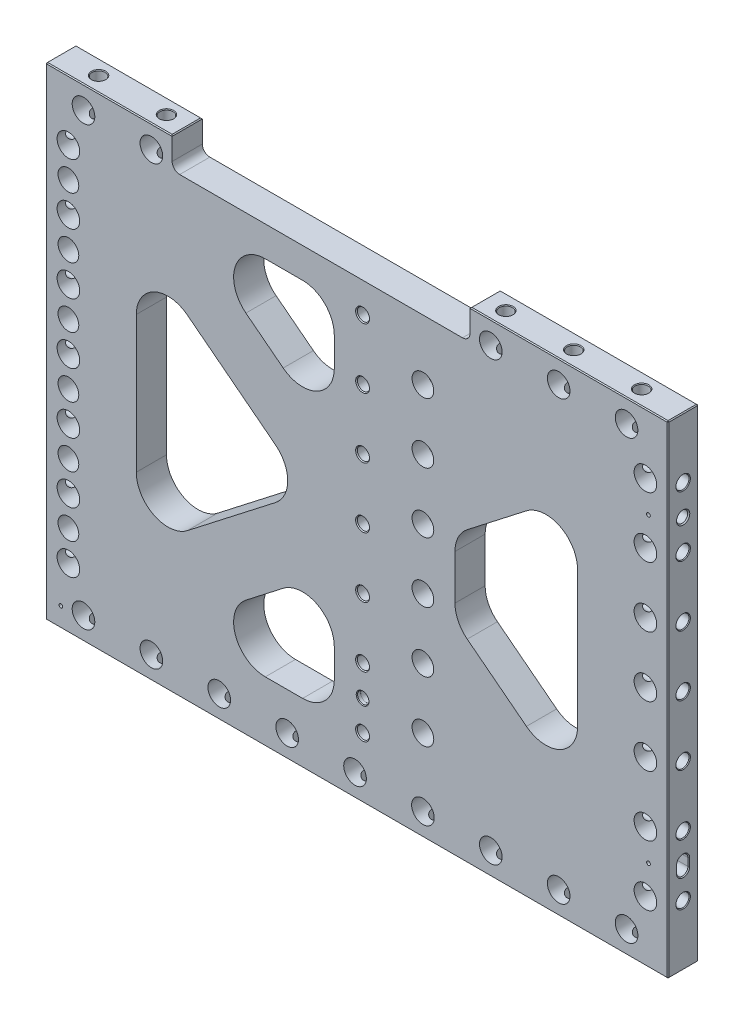
SolidWorks part; units mm, degrees
material "6061-T6 Al"
ref_plane "Front Plane" through (0, 0, 0) normal (0, 0, 1) x (1, 0, 0)
ref_plane "Top Plane" through (0, 0, 0) normal (0, 1, 0) x (1, 0, 0)
ref_plane "Right Plane" through (0, 0, 0) normal (1, 0, 0) x (0, 0, -1)
sketch "Sketch2" plane through (0, 0, 0) normal (0, 0, 1) x (1, 0, 0)
  line L0 (-261.9375, -203.2) -> (261.9375, 203.2) construction
  line L1 (-261.9375, 203.2) -> (261.9375, 203.2)
  line L2 (-261.9375, 203.2) -> (-261.9375, -203.2)
  line L3 (-261.9375, -203.2) -> (261.9375, -203.2)
  line L4 (261.9375, 203.2) -> (261.9375, -203.2)
  point P4 (0, 0)
  dimension "D1" = 523.875
  dimension "D2" = 406.4
extrude "Extrude1" add sketch "Sketch2" along normal mid plane 25.4
sketch "Sketch8" plane through (0, 0, 12.7) normal (0, 0, 1) x (1, 0, 0)
  line L0 (-261.9375, 203.2) -> (261.9375, -203.2) construction
  line L1 (261.9375, 203.2) -> (-261.9375, -203.2) construction
  line L2 (-185.7375, 111.9405) -> (-41.4392, 0)
  line L3 (-41.4392, 0) -> (-185.7375, -111.9405)
  line L4 (-185.7375, -111.9405) -> (-185.7375, 111.9405)
  line L5 (-155.0139, 152.4) -> (0, 32.1468)
  line L6 (0, 32.1468) -> (155.0139, 152.4)
  line L7 (155.0139, 152.4) -> (-155.0139, 152.4)
  line L8 (185.7375, 111.9405) -> (185.7375, -111.9405)
  line L9 (185.7375, -111.9405) -> (41.4392, 0)
  line L10 (41.4392, 0) -> (185.7375, 111.9405)
  line L11 (0, -32.1468) -> (-155.0139, -152.4)
  line L12 (-155.0139, -152.4) -> (155.0139, -152.4)
  line L13 (155.0139, -152.4) -> (0, -32.1468)
  line L14 (0, -32.1468) -> (-41.4392, 0) construction
  line L15 (-41.4392, 0) -> (0, 32.1468) construction
  line L20 (-261.9375, 203.2) -> (-261.9375, -203.2) construction
  line L21 (261.9375, 203.2) -> (-261.9375, 203.2) construction
  point P19 (-20.7196, 16.0734)
  point P23 (-20.7196, -16.0734)
  point P24 (-261.9375, 0)
  dimension "D1" = 50.8
  dimension "D2" = 76.2
  dimension "D3" = 50.8
extrude "Triangles -- Cut-Extrude2" cut sketch "Sketch8" against normal through all
fillet "Triangles -- Fillet1" radius 26.67 12 edges at (-185.7375, -111.9405, 0) (-41.4392, 0, 0) (-155.0139, -152.4, 0) (155.0139, -152.4, 0) (0, -32.1468, 0) (41.4392, 0, 0) (185.7375, -111.9405, 0) (185.7375, 111.9405, 0) (155.0139, 152.4, 0) (-155.0139, 152.4, 0) (0, 32.1468, 0) (-185.7375, 111.9405, 0)
sketch "Sketch14" plane through (0, 0, 12.7) normal (0, 0, 1) x (1, 0, 0)
  line L0 (261.9375, 203.2) -> (-261.9375, 203.2) construction
  line L1 (-19.05, 203.2) -> (19.05, 203.2)
  line L2 (-19.05, 203.2) -> (-19.05, -203.2)
  line L3 (-19.05, -203.2) -> (19.05, -203.2)
  line L4 (19.05, 203.2) -> (19.05, -203.2)
  line L5 (-261.9375, -203.2) -> (261.9375, -203.2) construction
  line L6 (19.05, 0) -> (-19.05, 0) construction
  point P10 (0, 0)
  dimension "D1" = 38.1
extrude "Extrude3" add sketch "Sketch14" against normal through all
fillet "Fillet1" radius 26.67 8 edges at (19.05, -152.4, 0) (-19.05, -152.4, 0) (-19.05, -46.925, 0) (19.05, -46.925, 0) (19.05, 46.925, 0) (19.05, 152.4, 0) (-19.05, 152.4, 0) (-19.05, 46.925, 0)
hole_wizard "3/4 (0.75) Diameter Hole1" positions "Sketch4" profile "Sketch3" hole size "3/4" standard "Ansi Inch" end condition through all
sketch "Sketch4" plane through (0, 0, 12.7) normal (0, 0, 1) x (1, 0, 0)
  line L3 (0, 0) -> (-242.8875, 0) construction
  line L6 (-261.9375, 203.2) -> (-261.9375, -203.2) construction
  point P0 (-242.8875, 0)
  dimension "D1" = 19.05
sketch "Sketch3" plane through (-242.8875, 0, 12.7) normal (1, 0, 0) x (0, -1, 0)
  line L0 (0, 0) -> (0, 25.4)
  line L1 (0, 25.4) -> (9.525, 25.4)
  line L2 (9.525, 25.4) -> (9.525, 0)
  line L5 (9.525, 0) -> (0, 0)
  line L11 (0, -6.35) -> (0, 107.95) construction
  dimension "Thru Hole Dia." = 19.05
  dimension "Thru Hole Depth" = 25.4
hole_wizard "7/16 (0.4375) Diameter Hole1" positions "Sketch6" profile "Sketch5" hole size "7/16" standard "Ansi Inch"
sketch "Sketch6" plane through (-261.9375, 0, 0) normal (-1, 0, 0) x (0, 0, 1)
  point P0 (0, 0)
sketch "Sketch5" plane through (-261.9375, 0, 0) normal (0, 1, 0) x (0, 0, 1)
  line L0 (0, 0) -> (0, 38.2635)
  line L1 (0, 38.2635) -> (5.5562, 34.925)
  line L2 (5.5562, 34.925) -> (5.5562, 0.6209)
  line L3 (5.5562, 0.6209) -> (6.096, 0)
  line L5 (6.096, 0) -> (0, 0)
  line L6 (-5.5562, 0.6209) -> (-6.096, 0) construction
  line L10 (0, 38.2635) -> (-5.5563, 34.925) construction
  line L11 (0, -6.35) -> (0, 107.95) construction
  dimension "Hole Dia." = 11.1125
  dimension "Hole Depth" = 34.925
  dimension "Near C'Sink Dia." = 12.192
  dimension "Near C'Sink Angle" = 82
  dimension "Drill Angle" = 118
pattern_linear "LPattern3" count 4 spacing 50.8 along (0, 1, 0) count 4 spacing 50.8 along (0, -1, 0) of "7/16 (0.4375) Diameter Hole1", "3/4 (0.75) Diameter Hole1"
mirror "Mirror1" about plane through (0, 0, 0) normal (1, 0, 0) of "LPattern3", "3/4 (0.75) Diameter Hole1", "7/16 (0.4375) Diameter Hole1"
hole_wizard "3/4 (0.75) Diameter Hole2" positions "Sketch11" profile "Sketch10" hole size "3/4" standard "Ansi Inch" end condition through all
sketch "Sketch11" plane through (0, 0, 12.7) normal (0, 0, 1) x (1, 0, 0)
  line L3 (-1.5875, -184.15) -> (-230.1875, -184.15) construction
  line L6 (-261.9375, -203.2) -> (261.9375, -203.2) construction
  point P25 (-230.1875, -184.15)
  dimension "D1" = 19.05
  dimension "D2" = 1.5875
  dimension "D3" = 228.6
sketch "Sketch10" plane through (-230.1875, -184.15, 12.7) normal (1, 0, 0) x (0, -1, 0)
  line L0 (0, 0) -> (0, 25.4)
  line L1 (0, 25.4) -> (9.525, 25.4)
  line L2 (9.525, 25.4) -> (9.525, 0)
  line L5 (9.525, 0) -> (0, 0)
  line L11 (0, -6.35) -> (0, 107.95) construction
  dimension "Thru Hole Dia." = 19.05
  dimension "Thru Hole Depth" = 25.4
hole_wizard "7/16 (0.4375) Diameter Hole2" positions "Sketch13" profile "Sketch12" hole size "7/16" standard "Ansi Inch"
sketch "Sketch13" plane through (0, -203.2, 0) normal (0, -1, 0) x (1, 0, 0)
  point P0 (-230.1875, 0)
sketch "Sketch12" plane through (-230.1875, -203.2, 0) normal (1, 0, 0) x (0, 0, -1)
  line L0 (0, 0) -> (0, 38.2635)
  line L1 (0, 38.2635) -> (5.5562, 34.925)
  line L2 (5.5562, 34.925) -> (5.5562, 0.6209)
  line L3 (5.5562, 0.6209) -> (6.096, 0)
  line L5 (6.096, 0) -> (0, 0)
  line L6 (-5.5562, 0.6209) -> (-6.096, 0) construction
  line L10 (0, 38.2635) -> (-5.5563, 34.925) construction
  line L11 (0, -6.35) -> (0, 107.95) construction
  dimension "Hole Dia." = 11.1125
  dimension "Hole Depth" = 34.925
  dimension "Near C'Sink Dia." = 12.192
  dimension "Near C'Sink Angle" = 82
  dimension "Drill Angle" = 118
pattern_linear "LPattern4" count 9 spacing 57.15 along (1, 0, 0) of "3/4 (0.75) Diameter Hole2", "7/16 (0.4375) Diameter Hole2"
hole_wizard "3/4 (0.75) Diameter Hole3" positions "Sketch34" profile "Sketch33" hole size "3/4" standard "Ansi Inch" end condition through all
sketch "Sketch34" plane through (0, 0, 12.7) normal (0, 0, 1) x (1, 0, 0)
  line L0 (-230.1875, 184.15) -> (-230.1875, 203.2) construction
  line L1 (261.9375, 203.2) -> (-261.9375, 203.2) construction
  line L4 (-230.1875, -184.15) -> (-230.1875, -203.2) construction
  line L5 (-261.9375, -203.2) -> (261.9375, -203.2) construction
  point P0 (-230.1875, 184.15)
sketch "Sketch33" plane through (-230.1875, 184.15, 12.7) normal (1, 0, 0) x (0, -1, 0)
  line L0 (0, 0) -> (0, 25.4)
  line L1 (0, 25.4) -> (9.525, 25.4)
  line L2 (9.525, 25.4) -> (9.525, 0)
  line L5 (9.525, 0) -> (0, 0)
  line L11 (0, -6.35) -> (0, 107.95) construction
  dimension "Thru Hole Dia." = 19.05
  dimension "Thru Hole Depth" = 25.4
hole_wizard "7/16 (0.4375) Diameter Hole3" positions "Sketch36" profile "Sketch35" hole size "7/16" standard "Ansi Inch"
sketch "Sketch36" plane through (0, 203.2, 0) normal (0, 1, 0) x (-1, 0, 0)
  point P0 (230.1875, 0)
sketch "Sketch35" plane through (-230.1875, 203.2, 0) normal (1, 0, 0) x (0, 0, 1)
  line L0 (0, 0) -> (0, 38.2635)
  line L1 (0, 38.2635) -> (5.5562, 34.925)
  line L2 (5.5562, 34.925) -> (5.5562, 0.6209)
  line L3 (5.5562, 0.6209) -> (6.096, 0)
  line L5 (6.096, 0) -> (0, 0)
  line L6 (-5.5562, 0.6209) -> (-6.096, 0) construction
  line L10 (0, 38.2635) -> (-5.5563, 34.925) construction
  line L11 (0, -6.35) -> (0, 107.95) construction
  dimension "Hole Dia." = 11.1125
  dimension "Hole Depth" = 34.925
  dimension "Near C'Sink Dia." = 12.192
  dimension "Near C'Sink Angle" = 82
  dimension "Drill Angle" = 118
pattern_linear "LPattern6" count 9 spacing 57.15 along (1, 0, 0) skipping (2, 0), (3, 0), (4, 0), (5, 0) of "3/4 (0.75) Diameter Hole3", "7/16 (0.4375) Diameter Hole3"
hole_wizard "CBORE for 3/8 Socket Head Cap Screw2" positions "Sketch16" profile "Sketch15" counterbore size "3/8" standard "Ansi Inch" end condition through all
sketch "Sketch16" plane through (70.8961, 59.1665, -12.7) normal (0, 0, 1) x (1, 0, 0)
  point P1 (-66.1336, -59.1665)
  dimension "D1" = 4.7625
sketch "Sketch15" plane through (4.7625, 0, -12.7) normal (1, 0, 0) x (0, 1, 0)
  line L0 (0, 0) -> (0, 25.4)
  line L1 (5.1587, 24.614) -> (5.842, 25.4)
  line L2 (5.1587, 24.614) -> (5.1587, 10.668)
  line L3 (5.1587, 10.668) -> (8.7312, 10.668)
  line L4 (8.7312, 10.668) -> (8.7312, 0)
  line L5 (8.7312, 0) -> (0, 0)
  line L11 (0, -6.35) -> (0, 107.95) construction
  line L12 (5.842, 25.4) -> (0, 25.4)
  line L13 (-5.1587, 24.614) -> (-5.842, 25.4) construction
  dimension "Thru Hole Dia." = 10.3175
  dimension "Thru Hole Depth" = 25.4
  dimension "C'Bore Dia." = 17.4625
  dimension "C'Bore Depth" = 10.668
  dimension "Far C'Sink Dia." = 11.684
  dimension "Far C'Sink Angle" = 82
pattern_linear "LPattern5" count 4 spacing 50.8 along (0, -1, 0) count 4 spacing 50.8 along (0, 1, 0) of "CBORE for 3/8 Socket Head Cap Screw2"
hole_wizard "CBORE for 3/8 Socket Head Cap Screw1" positions "Sketch18" profile "Sketch17" counterbore size "3/8" standard "Ansi Inch" end condition through all
sketch "Sketch18" plane through (0, 0, 12.7) normal (0, 0, 1) x (1, 0, 0)
  line L0 (-242.8875, 152.4) -> (-242.8875, 101.6) construction
  line L1 (-242.8875, 101.6) -> (-242.8875, 50.8) construction
  line L2 (-242.8875, 50.8) -> (-242.8875, 0) construction
  line L3 (-242.8875, 0) -> (-242.8875, -50.8) construction
  line L4 (-242.8875, -50.8) -> (-242.8875, -101.6) construction
  line L5 (-242.8875, -101.6) -> (-242.8875, -152.4) construction
  point P0 (-242.8875, 127)
  point P32 (-242.8875, 76.2)
  point P34 (-242.8875, 25.4)
  point P36 (-242.8875, -25.4)
  point P38 (-242.8875, -76.2)
  point P40 (-242.8875, -127)
sketch "Sketch17" plane through (-242.8875, 127, 12.7) normal (1, 0, 0) x (0, -1, 0)
  line L0 (0, 0) -> (0, 25.4)
  line L1 (5.1587, 24.614) -> (5.842, 25.4)
  line L2 (5.1587, 24.614) -> (5.1587, 12.7)
  line L3 (5.1587, 12.7) -> (8.7312, 12.7)
  line L4 (8.7312, 12.7) -> (8.7312, 0)
  line L5 (8.7312, 0) -> (0, 0)
  line L11 (0, -6.35) -> (0, 107.95) construction
  line L12 (5.842, 25.4) -> (0, 25.4)
  line L13 (-5.1587, 24.614) -> (-5.842, 25.4) construction
  dimension "Thru Hole Dia." = 10.3175
  dimension "Thru Hole Depth" = 25.4
  dimension "C'Bore Dia." = 17.4625
  dimension "C'Bore Depth" = 12.7
  dimension "Far C'Sink Dia." = 11.684
  dimension "Far C'Sink Angle" = 82
sketch "Sketch19" plane through (0, 203.2, 0) normal (0, 1, 0) x (1, 0, 0)
  line L0 (261.9375, -12.7) -> (-261.9375, -12.7) construction
  line L1 (95.2373, -12.7) -> (-155.5623, -12.7)
  line L2 (95.2373, -12.7) -> (95.2373, 12.7)
  line L3 (95.2373, 12.7) -> (-155.5623, 12.7)
  line L4 (-155.5623, -12.7) -> (-155.5623, 12.7)
  line L5 (261.9375, 12.7) -> (-261.9375, 12.7) construction
  line L6 (-261.9375, -12.7) -> (-261.9375, 12.7) construction
  dimension "D1" = 106.3752
  dimension "D2" = 357.1748
extrude "Cut-Extrude1" cut sketch "Sketch19" against normal blind 25.4
fillet "Fillet2" radius 6.35 2 edges at (-155.5623, 177.8, 0) (95.2373, 177.8, 0)
sketch "Sketch21" plane through (0, 0, 12.7) normal (0, 0, 1) x (1, 0, 0)
  line L1 (77.1234, 152.4) -> (19.05, 152.4)
  line L3 (77.1234, -152.4) -> (19.05, -152.4)
  line L4 (19.05, 152.4) -> (19.05, -152.4)
  line L5 (77.1234, 152.4) -> (45.72, 152.4) construction
  line L6 (19.05, 101.3686) -> (19.05, 125.73) construction
  line L7 (93.4706, -104.6574) -> (62.0673, -80.296) construction
  line L8 (62.0673, 80.296) -> (93.4706, 104.6574) construction
  line L9 (93.4706, -104.6574) -> (82.55, -96.1856)
  line L10 (82.55, 96.1856) -> (93.4706, 104.6574)
  line L11 (82.55, 96.1856) -> (82.55, -96.1856)
  arc A0 (77.1234, -152.4) -> (93.4706, -104.6574) centre (77.1234, -125.73) ccw construction
  arc A1 (93.4706, 104.6574) -> (77.1234, 152.4) centre (77.1234, 125.73) ccw construction
  arc A2 (77.1234, -152.4) -> (93.4706, -104.6574) centre (77.1234, -125.73) ccw
  arc A3 (93.4706, 104.6574) -> (77.1234, 152.4) centre (77.1234, 125.73) ccw
  dimension "D1" = 82.55
extrude "Extrude5" add sketch "Sketch21" against normal through all
fillet "Fillet3" radius 26.67 2 edges at (82.55, 31.892, 0) (82.55, -31.892, 0)
hole_wizard "CBORE for 3/8 Socket" positions "Sketch23" profile "Sketch22" counterbore size "3/8" standard "Ansi Inch" end condition through all
sketch "Sketch23" plane through (0, 0, 12.7) normal (0, 0, 1) x (1, 0, 0)
  line L0 (55.5625, -127) -> (55.5625, -76.2) construction
  line L1 (55.5625, -76.2) -> (55.5625, -25.4) construction
  line L2 (55.5625, -25.4) -> (55.5625, 25.4) construction
  line L3 (55.5625, 25.4) -> (55.5625, 76.2) construction
  line L4 (55.5625, 76.2) -> (55.5625, 127) construction
  line L7 (-261.9375, -203.2) -> (261.9375, -203.2) construction
  point P1 (55.5625, 127)
  point P4 (55.5625, 76.2)
  point P7 (55.5625, 25.4)
  point P10 (55.5625, -25.4)
  point P13 (55.5625, -76.2)
  point P16 (55.5625, -127)
  dimension "D1" = 50.8
  dimension "D2" = 76.2
  dimension "D3" = 55.5625
sketch "Sketch22" plane through (55.5625, 127, 12.7) normal (1, 0, 0) x (0, -1, 0)
  line L0 (0, 0) -> (0, 25.4)
  line L1 (5.5562, 24.4869) -> (6.35, 25.4)
  line L2 (5.5562, 24.4869) -> (5.5563, 12.7)
  line L3 (5.5563, 12.7) -> (9.1281, 12.7)
  line L4 (9.1281, 12.7) -> (9.1281, 0)
  line L5 (9.1281, 0) -> (0, 0)
  line L11 (0, -6.35) -> (0, 107.95) construction
  line L12 (6.35, 25.4) -> (0, 25.4)
  line L13 (-5.5563, 24.4869) -> (-6.35, 25.4) construction
  dimension "Thru Hole Dia." = 11.1125
  dimension "Thru Hole Depth" = 25.4
  dimension "C'Bore Dia." = 18.2562
  dimension "C'Bore Depth" = 12.7
  dimension "Far C'Sink Dia." = 12.7
  dimension "Far C'Sink Angle" = 82
hole_wizard "3/8 (0.376) Pin Locate1" positions "Sketch25" profile "Sketch24" hole size "3/8" standard "Ansi Inch"
sketch "Sketch25" plane through (261.9375, 0, 0) normal (1, 0, 0) x (0, 0, -1)
  line L0 (0, 152.4) -> (0, 101.6) construction
  point P0 (0, 127)
sketch "Sketch24" plane through (261.9375, 127, 0) normal (0, 1, 0) x (0, 0, -1)
  line L0 (0, 0) -> (0, 21.9192)
  line L1 (0, 21.9192) -> (4.7752, 19.05)
  line L2 (4.7752, 19.05) -> (4.7752, 0.935)
  line L3 (4.7752, 0.935) -> (5.588, 0)
  line L5 (5.588, 0) -> (0, 0)
  line L6 (-4.7752, 0.935) -> (-5.588, 0) construction
  line L10 (0, 21.9192) -> (-4.7752, 19.05) construction
  line L11 (0, -6.35) -> (0, 107.95) construction
  dimension "Hole Dia." = 9.5504
  dimension "Hole Depth" = 19.05
  dimension "Near C'Sink Dia." = 11.176
  dimension "Near C'Sink Angle" = 82
  dimension "Drill Angle" = 118
sketch "Sketch26" plane through (261.9375, 0, 0) normal (1, 0, 0) x (0, 0, -1)
  line L0 (0, -152.4) -> (0, -127) construction
  line L1 (0, -127) -> (0, -101.6) construction
  line L2 (0, -123.825) -> (0, -130.175) construction
  line L3 (-4.7752, -123.825) -> (-4.7752, -130.175)
  line L4 (4.7752, -123.825) -> (4.7752, -130.175)
  arc A0 (-4.7752, -123.825) -> (4.7752, -123.825) centre (0, -123.825) cw
  arc A1 (-4.7752, -130.175) -> (4.7752, -130.175) centre (0, -130.175) ccw
  point P8 (0, -127)
  dimension "D1" = 6.35
  dimension "D2" = 9.5504
  dimension "D3" = 4.7752
extrude "Slot Locate1" cut sketch "Sketch26" against normal blind 19.05
chamfer "Chamfer1" distance 0.762 angle 45 4 edges at (261.9375, -119.0498, 0) (261.9375, -127, 4.7752) (261.9375, -127, -4.7752) (261.9375, -134.9502, 0)
hole_wizard "3/8 (0.375) Pin + Lead-In Hole1" positions "Sketch28" profile "Sketch27" counterbore size "3/8" standard "Ansi Inch"
sketch "Sketch28" plane through (0, -203.2, 0) normal (0, -1, 0) x (1, 0, 0)
  line L0 (-261.9375, 0) -> (-249.2375, 0) construction
  line L1 (-261.9375, 12.7) -> (-261.9375, -12.7) construction
  point P0 (-249.2375, 0)
  dimension "D1" = 12.7
sketch "Sketch27" plane through (-249.2375, -203.2, 0) normal (1, 0, 0) x (0, 0, -1)
  line L0 (0, 0) -> (0, 21.9116)
  line L1 (0, 21.9116) -> (4.7625, 19.05)
  line L2 (4.7625, 19.05) -> (4.7625, 3.175)
  line L3 (4.7625, 3.175) -> (4.7879, 3.175)
  line L5 (4.7879, 3.175) -> (4.7879, 0.6282)
  line L6 (4.7879, 0.6282) -> (5.334, 0)
  line L7 (5.334, 0) -> (0, 0)
  line L8 (-4.7879, 0.6282) -> (-5.334, 0) construction
  line L10 (0, 21.9116) -> (-4.7625, 19.05) construction
  line L11 (0, -6.35) -> (0, 107.95) construction
  dimension "Hole Dia." = 9.525
  dimension "Hole Depth" = 19.05
  dimension "C'Bore Dia." = 9.5758
  dimension "C'Bore Depth" = 3.175
  dimension "Near C'Sink Dia." = 10.668
  dimension "Near C'Sink Angle" = 82
  dimension "Drill Angle" = 118
hole_wizard "1/8 (0.125) Diameter Hole1" positions "Sketch30" profile "Sketch29" hole size "1/8" standard "Ansi Inch"
sketch "Sketch30" plane through (0, 0, 12.7) normal (0, 0, 1) x (1, 0, 0)
  line L0 (242.8875, 131.7752) -> (242.8875, 122.2248) construction
  line L1 (242.8875, -123.825) -> (242.8875, -130.175) construction
  line L3 (242.8875, 131.7752) -> (242.8875, 122.2248)
  line L4 (242.8875, -123.825) -> (242.8875, -130.175)
  line L6 (-249.2375, -184.15) -> (-249.2375, -186.69) construction
  line L9 (242.8875, -127) -> (245.4275, -127) construction
  line L12 (242.8875, 127) -> (245.4275, 127) construction
  line L13 (-244.475, -184.15) -> (-254, -184.15) construction
  line L14 (-244.475, -184.15) -> (-254, -184.15)
  point P0 (-249.2375, -186.69)
  point P24 (245.4275, -127)
  point P26 (245.4275, 127)
  dimension "D1" = 2.54
sketch "Sketch29" plane through (-249.2375, -186.69, 12.7) normal (1, 0, 0) x (0, -1, 0)
  line L0 (0, 0) -> (0, 10.6059)
  line L1 (0, 10.6059) -> (1.5875, 9.652)
  line L2 (1.5875, 9.652) -> (1.5875, 0)
  line L5 (1.5875, 0) -> (0, 0)
  line L10 (0, 10.6059) -> (-1.5875, 9.652) construction
  line L11 (0, -6.35) -> (0, 107.95) construction
  dimension "Hole Dia." = 3.175
  dimension "Hole Depth" = 9.652
  dimension "Drill Angle" = 118
hole_wizard "3/8 (0.375) Pin + Lead-In Hole2" positions "Sketch32" profile "Sketch31" counterbore size "3/8" standard "Ansi Inch" end condition through all
sketch "Sketch32" plane through (0, 0, 12.7) normal (0, 0, 1) x (1, 0, 0)
  line L0 (4.7625, 0) -> (4.7625, -127) construction
  point P0 (4.7625, -127)
  dimension "D1" = 127
sketch "Sketch31" plane through (4.7625, -127, 12.7) normal (1, 0, 0) x (0, -1, 0)
  line L0 (0, 0) -> (0, 25.4)
  line L1 (0, 25.4) -> (4.7625, 25.4)
  line L3 (4.7625, 25.4) -> (4.7625, 3.175)
  line L4 (4.7879, 3.175) -> (4.7625, 3.175)
  line L5 (4.7879, 3.175) -> (4.7879, 0.6282)
  line L6 (4.7879, 0.6282) -> (5.334, 0)
  line L7 (5.334, 0) -> (0, 0)
  line L8 (-4.7879, 0.6282) -> (-5.334, 0) construction
  line L11 (0, -6.35) -> (0, 107.95) construction
  dimension "Thru Hole Dia." = 9.525
  dimension "Thru Hole Depth" = 25.4
  dimension "C'Bore Dia." = 9.5758
  dimension "C'Bore Depth" = 3.175
  dimension "Near C'Sink Dia." = 10.668
  dimension "Near C'Sink Angle" = 82
chamfer "Chamfer2" distance 0.762 angle 45 16 edges at (-261.9375, 0, 12.7) (261.9375, 0, -12.7) (261.9375, 203.2, 0) (178.5874, 203.2, -12.7) (95.2373, 203.2, 0) (178.5874, 203.2, 12.7) (261.9375, 0, 12.7) (261.9375, -203.2, 0) (0, -203.2, 12.7) (-261.9375, -203.2, 0) (0, -203.2, -12.7) (-261.9375, 0, -12.7) (-155.5623, 203.2, 0) (-208.7499, 203.2, -12.7) (-261.9375, 203.2, 0) (-208.7499, 203.2, 12.7)
